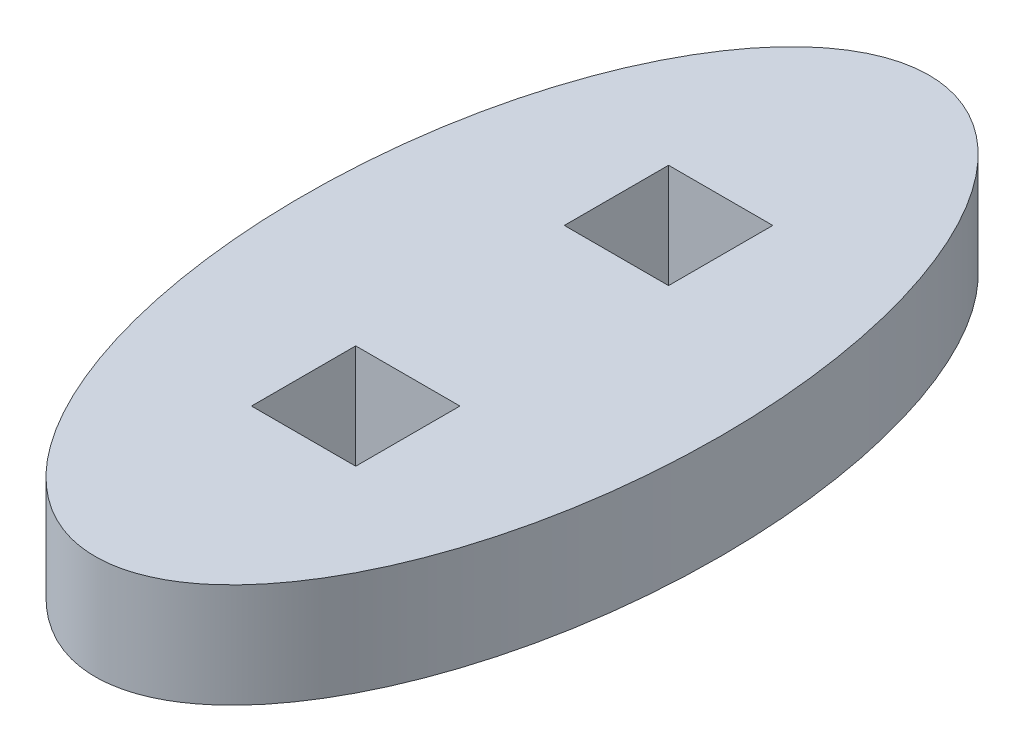
SolidWorks part; units mm, degrees
ref_plane "Front Plane" through (0, 0, 0) normal (0, 0, 1) x (1, 0, 0)
ref_plane "Top Plane" through (0, 0, 0) normal (0, 1, 0) x (1, 0, 0)
ref_plane "Right Plane" through (0, 0, 0) normal (1, 0, 0) x (0, 0, -1)
sketch "Sketch1" plane through (0, 0, 0) normal (0, 1, 0) x (1, 0, 0)
  ellipse E0 centre (0, 0) end of major axis (0, 12.7) minor radius 6.35
  dimension "D1" = 6.35
  dimension "D2" = 12.7
extrude "Boss-Extrude1" add sketch "Sketch1" along normal blind 3.175
sketch "Sketch2" plane through (0, 3.175, 0) normal (0, 1, 0) x (1, 0, 0)
  line L0 (0, -12.7) -> (0, 12.7) construction
  line L1 (-6.35, 0) -> (6.35, 0) construction
  line L2 (-1.5875, 6.355) -> (-1.5875, 3.18)
  line L3 (-1.5875, -3.175) -> (1.5875, -3.175)
  line L4 (-1.5875, -3.175) -> (-1.5875, -6.35)
  line L5 (-1.5875, -6.35) -> (1.5875, -6.35)
  line L6 (1.5875, -3.175) -> (1.5875, -6.35)
  line L7 (-1.5875, -3.175) -> (1.5875, -6.35) construction
  line L8 (-1.5875, -6.35) -> (1.5875, -3.175) construction
  line L9 (-1.5875, 6.355) -> (1.5875, 6.355)
  line L10 (1.5875, 6.355) -> (1.5875, 3.18)
  line L11 (-1.5875, 3.18) -> (1.5875, 3.18)
  ellipse E0 centre (0, 0) end of major axis (0, 12.7) minor radius 6.35 construction
  point P11 (0, -4.7625)
  dimension "D1" = 3.175
  dimension "D2" = 3.175
  dimension "D3" = 3.175
  dimension "D4" = 2
extrude "Cut-Extrude1" cut sketch "Sketch2" against normal through all
